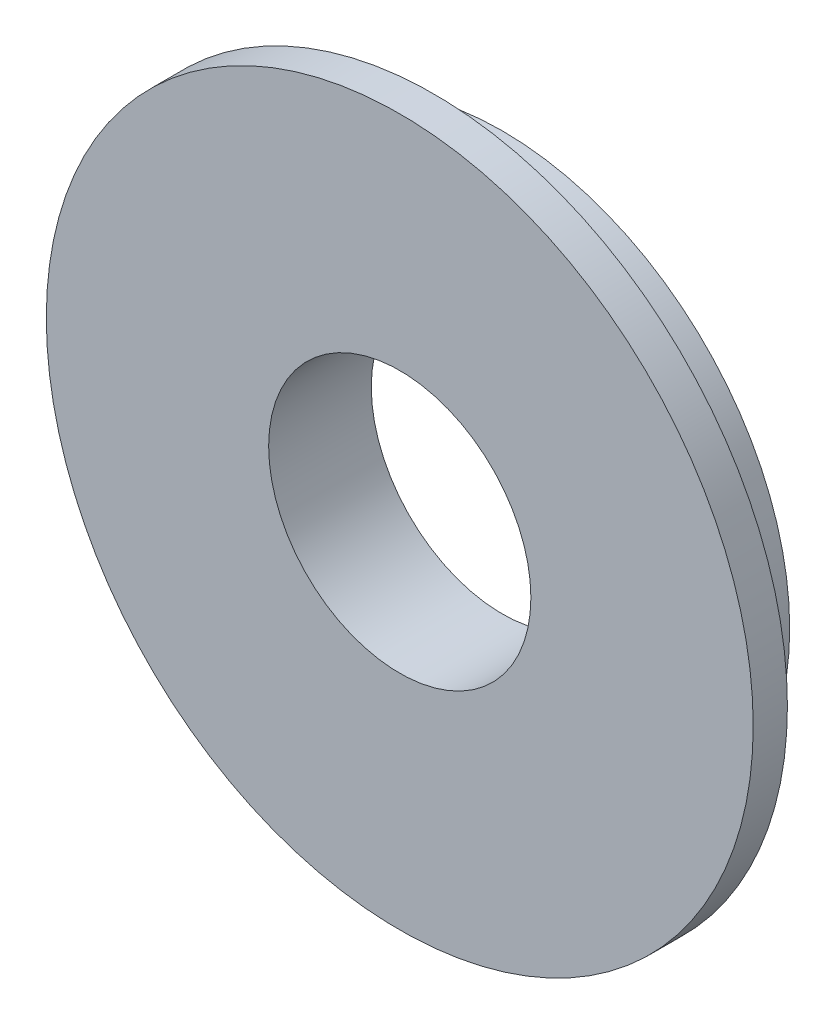
SolidWorks part; units mm, degrees
ref_plane "Front Plane" through (0, 0, 0) normal (0, 0, 1) x (1, 0, 0)
ref_plane "Top Plane" through (0, 0, 0) normal (0, 1, 0) x (1, 0, 0)
ref_plane "Right Plane" through (0, 0, 0) normal (1, 0, 0) x (0, 0, -1)
sketch "Sketch1" plane through (0, 0, 0) normal (0, 0, 1) x (1, 0, 0)
  circle A0 centre (0, 0) radius 15.5
  circle A1 centre (0, 0) radius 5.75
  dimension "D1" = 31
  dimension "D2" = 11.5
extrude "Boss-Extrude1" add sketch "Sketch1" along normal blind 1.5
sketch "Sketch2" plane through (0, 0, 0) normal (0, 0, -1) x (-1, 0, 0)
  circle A0 centre (0, 0) radius 12.6
  circle A1 centre (0, 0) radius 5.75 construction
  circle A2 centre (0, 0) radius 5.75
  dimension "D1" = 25.2
extrude "Boss-Extrude2" add sketch "Sketch2" along normal blind 3
